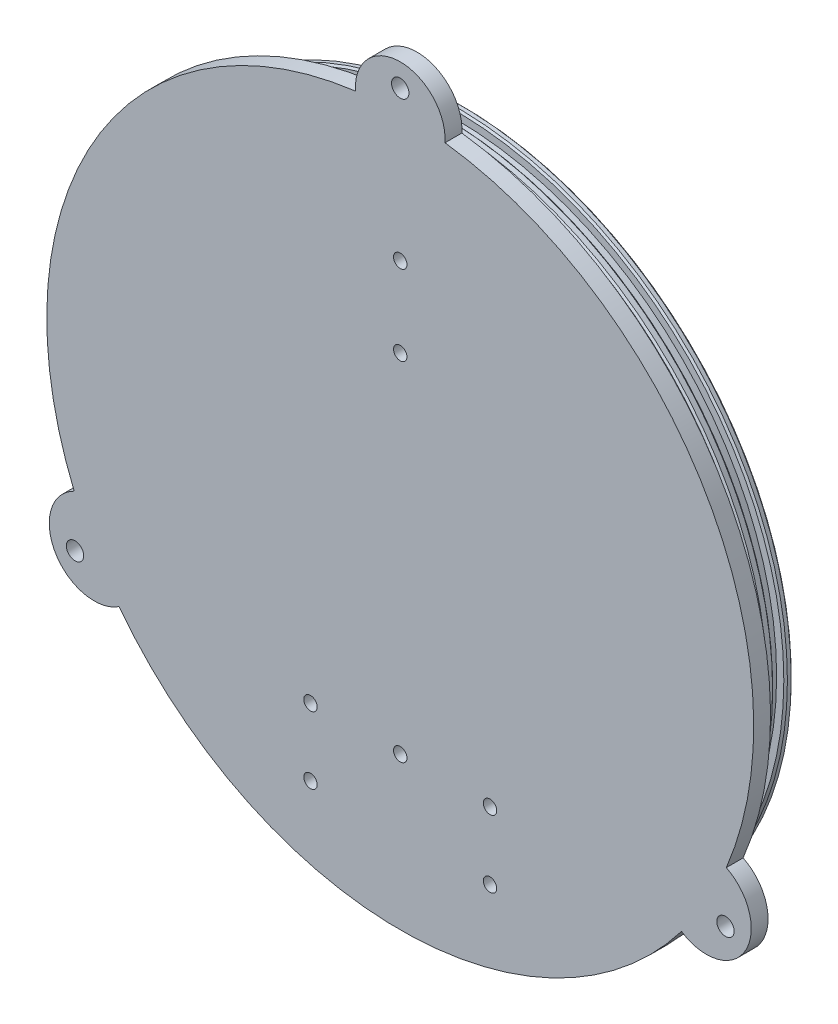
SolidWorks part; units mm, degrees
material "6061 Alloy"
ref_plane "Front Plane" through (0, 0, 0) normal (0, 0, 1) x (1, 0, 0)
ref_plane "Top Plane" through (0, 0, 0) normal (0, 1, 0) x (1, 0, 0)
ref_plane "Right Plane" through (0, 0, 0) normal (1, 0, 0) x (0, 0, -1)
sketch "Sketch1" plane through (0, 0, 0) normal (0, 0, 1) x (1, 0, 0)
  circle A0 centre (0, 0) radius 100.0125
extrude "Extrude1" add sketch "Sketch1" along normal blind 4.7625
sketch "Sketch2" plane through (0, 0, 0) normal (0, 0, -1) x (-1, 0, 0)
  circle A0 centre (0, 0) radius 93.6625
extrude "Extrude2" add sketch "Sketch2" along normal blind 12.7
sketch "Sketch3" plane through (0, 0, -12.7) normal (0, 0, -1) x (-1, 0, 0)
  circle A0 centre (0, 0) radius 87.3125
extrude "Cut-Extrude1" cut sketch "Sketch3" against normal blind 12.7
sketch "Sketch4" plane through (0, 0, 0) normal (1, 0, 0) x (0, 0, -1)
  line L0 (12.7, 93.6625) -> (0, 93.6625) construction
  line L1 (1.8084, 93.6625) -> (4.9834, 93.6625)
  line L2 (1.8084, 93.6625) -> (1.8084, 91.1225)
  line L3 (1.8084, 91.1225) -> (4.9834, 91.1225)
  line L4 (4.9834, 93.6625) -> (4.9834, 91.1225)
  line L5 (0, 0) -> (42.3826, 0) construction
  line L6 (7.4409, 93.6625) -> (10.6159, 93.6625)
  line L7 (7.4409, 93.6625) -> (7.4409, 91.1225)
  line L8 (7.4409, 91.1225) -> (10.6159, 91.1225)
  line L9 (10.6159, 93.6625) -> (10.6159, 91.1225)
  dimension "D1" = 2.54
  dimension "D2" = 3.175
revolve "Cut-Revolve1" cut sketch "Sketch4" angle 360 about L5
sketch "Sketch5" plane through (0, 0, 4.7625) normal (0, 0, 1) x (1, 0, 0)
  line L0 (0, 100.0125) -> (0, 0) construction
  line L1 (0, 0) -> (86.6134, -50.0062) construction
  line L2 (0, 0) -> (-86.6134, -50.0062) construction
  circle A0 centre (0, 0) radius 100.0125 construction
  arc A1 (-12.6744, 99.2062) -> (12.6744, 99.2062) centre (0, 100.0125) cw
  arc A2 (92.2522, -38.6267) -> (79.5779, -60.5794) centre (86.6134, -50.0062) cw
  arc A3 (-79.5779, -60.5794) -> (-92.2522, -38.6267) centre (-86.6134, -50.0062) cw
  arc A4 (-12.6744, 99.2062) -> (12.6744, 99.2062) centre (0, 0) cw
  arc A5 (79.5779, -60.5794) -> (92.2522, -38.6267) centre (0, 0) ccw
  arc A6 (-79.5779, -60.5794) -> (-92.2522, -38.6267) centre (0, 0) cw
  dimension "D1" = 120
  dimension "D3" = 12.7
  dimension "D4" = 12.7
  dimension "D5" = 12.7
  dimension "D2" = 120
extrude "Extrude3" add sketch "Sketch5" against normal up to surface (4.7625 mm away) up to face at (100.0125, 0, 0)
sketch "Sketch7" plane through (0, 0, 4.7625) normal (0, 0, 1) x (1, 0, 0)
  line L0 (-130.4405, -75.3098) -> (0, 0) construction
  line L1 (0, 0) -> (0, 112.7125) construction
  line L2 (0, 0) -> (145.4143, -83.955) construction
  arc A1 (12.6744, 99.2062) -> (-12.6744, 99.2062) centre (0, 100.0125) ccw construction
hole_wizard "#10 (0.1935) Diameter Hole1" positions "3DSketch1" profile "Sketch8" hole size "#10" standard "Ansi Inch"
sketch3d "3DSketch1"
  line L0 (0, 0, 4.7625) -> (0, 112.7125, 4.7625) construction
  line L1 (-130.4405, -75.3098, 4.7625) -> (0, 0, 4.7625) construction
  line L2 (0, 0, 4.7625) -> (145.4143, -83.955, 4.7625) construction
  point P0 (0, 106.2558, 4.7625)
  point P4 (-92.0202, -53.1279, 4.7625)
  point P8 (92.0202, -53.1279, 4.7625)
  dimension "D1" = 106.3625
  dimension "D2" = 106.3625
  dimension "D3" = 106.3625
sketch "Sketch8" plane through (0, 106.2558, 4.7625) normal (1, 0, 0) x (0, -1, 0)
  line L0 (0, 0) -> (0, 331.6766)
  line L1 (0, 331.6766) -> (2.4574, 330.2)
  line L2 (2.4574, 330.2) -> (2.4574, 0)
  line L5 (2.4574, 0) -> (0, 0)
  line L10 (0, 331.6766) -> (-2.4575, 330.2) construction
  line L11 (0, -6.35) -> (0, 107.95) construction
  dimension "Hole Dia." = 4.9149
  dimension "Hole Depth" = 330.2
  dimension "Drill Angle" = 118
chamfer "Chamfer1" distance 0.508 angle 45 5 edges at (-93.6625, 0, -12.7) (93.6625, 0, -10.6159) (93.6625, 0, -7.4409) (93.6625, 0, -4.9834) (93.6625, 0, -1.8084)
hole_wizard "#6 Clearance Hole1" positions "3DSketch2" profile "Sketch9" hole size "#6" standard "Ansi Inch"
sketch3d "3DSketch2"
  line L3 (0, 100.0125, 4.7625) -> (0, -100.0125, 4.7625) construction
  line L4 (0, 100.0125, 0) -> (0, 100.0125, 4.7625) construction
  arc A0 (-79.5779, -60.5794, 4.7625) -> (79.5779, -60.5794, 4.7625) centre (0, 0, 4.7625) ccw construction
  point P27 (0, 0, 104.775)
  point P33 (0, 63.9528, 4.7625)
  point P35 (0, 41.3468, 4.7625)
  point P37 (0, -56.9512, 4.7625)
  dimension "D1" = 22.606
  dimension "D2" = 98.298
  dimension "D3" = 57.15
sketch "Sketch9" plane through (0, 63.9528, 4.7625) normal (1, 0, 0) x (0, -1, 0)
  line L0 (0, 0) -> (0, 7.4908)
  line L1 (0, 7.4908) -> (1.8986, 6.35)
  line L2 (1.8986, 6.35) -> (1.8986, 0)
  line L5 (1.8986, 0) -> (0, 0)
  line L10 (0, 7.4908) -> (-1.8987, 6.35) construction
  line L11 (0, -6.35) -> (0, 107.95) construction
  dimension "Hole Dia." = 3.7973
  dimension "Hole Depth" = 6.35
  dimension "Drill Angle" = 118
hole_wizard "#6 Clearance Hole2" positions "3DSketch3" profile "Sketch10" hole size "#6" standard "Ansi Inch"
sketch3d "3DSketch3"
  line L0 (0, 0, 0) -> (0, -31.4514, 0) construction
  line L2 (0, 0, 0) -> (35.3643, 0, 0) construction
  point P15 (25.4, -57.15, 0)
  point P17 (-25.4, -57.15, 0)
  point P19 (25.4, -76.2, 0)
  point P21 (-25.4, -76.2, 0)
  dimension "D5" = 19.05
  dimension "D6" = 50.8
  dimension "D7" = 25.4
  dimension "D8" = 57.15
sketch "Sketch10" plane through (25.4, -57.15, 0) normal (1, 0, 0) x (0, 1, 0)
  line L0 (0, 0) -> (0, 26.5408)
  line L1 (0, 26.5408) -> (1.8986, 25.4)
  line L2 (1.8986, 25.4) -> (1.8986, 0)
  line L5 (1.8986, 0) -> (0, 0)
  line L10 (0, 26.5408) -> (-1.8987, 25.4) construction
  line L11 (0, -6.35) -> (0, 107.95) construction
  dimension "Hole Dia." = 3.7973
  dimension "Hole Depth" = 25.4
  dimension "Drill Angle" = 118
